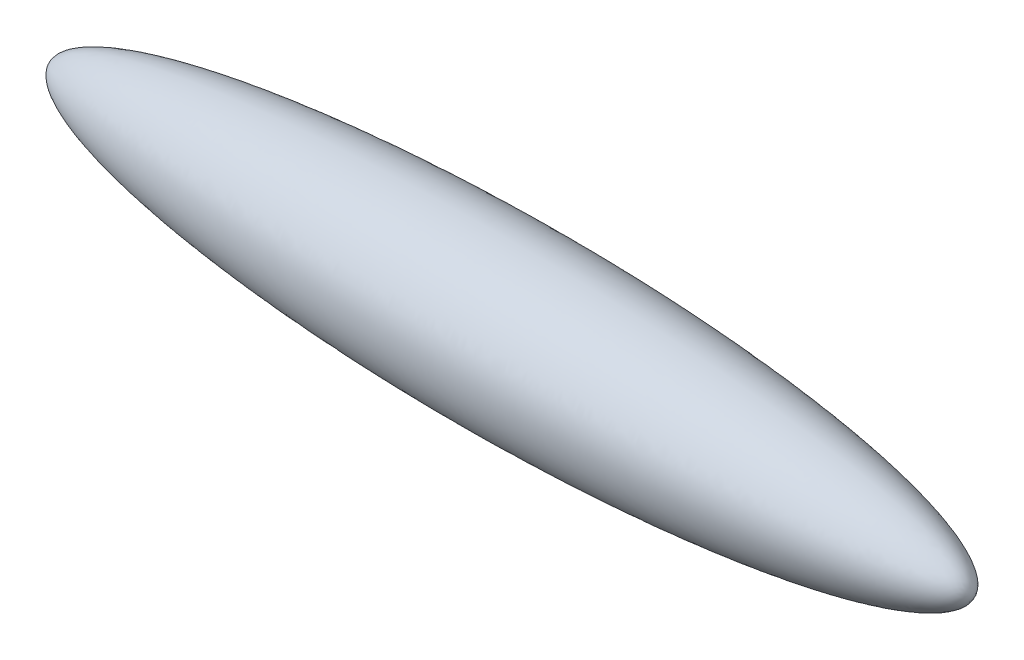
SolidWorks part; units mm, degrees
ref_plane "Plano frontal" through (0, 0, 0) normal (0, 0, 1) x (1, 0, 0)
ref_plane "Plano superior" through (0, 0, 0) normal (0, 1, 0) x (1, 0, 0)
ref_plane "Plano direito" through (0, 0, 0) normal (1, 0, 0) x (0, 0, -1)
ref_axis "Axis1" through (4.5739, 0, 0) along (-1, 0, 0)
sketch "Sketch3" plane through (0, 0, 0) normal (0, 0, 1) x (1, 0, 0)
  line L0 (686, 0) -> (-686, 0)
  spline S0 degree 4 poles (-686, 0) (-685.9997, 0.6998) (-685.9315, 2.0942) (-685.5565, 4.638) (-684.2628, 8.6049) (-681.9683, 12.7129) (-678.7283, 16.7962) (-674.2901, 21.2055) (-668.9242, 25.5245) (-663.2572, 29.309) (-657.4318, 32.6986) (-651.3994, 35.8922) (-643.1035, 39.9133) (-631.1855, 44.9636) (-615.5232, 50.6535) (-597.1722, 56.3985) (-578.3815, 61.5763) (-558.3108, 66.522) (-539.9291, 70.5832) (-523.2886, 73.9541) (-505.4444, 77.3208) (-487.5599, 80.4679) (-460.6708, 84.821) (-424.7132, 89.939) (-382.6513, 95.0696) (-334.4738, 99.9694) (-274.1554, 105.0481) (-201.6603, 109.6504) (-116.9816, 113.1179) (-32.2446, 114.5222) (40.3939, 114.3107) (100.9139, 113.1788) (149.3154, 111.6868) (197.6944, 109.5853) (246.0413, 106.8402) (294.3442, 103.4031) (342.5875, 99.2061) (390.7495, 94.1546) (432.7922, 88.8675) (468.7271, 83.5905) (498.5781, 78.5964) (522.3867, 74.1899) (546.1018, 69.302) (566.7424, 64.5181) (584.3238, 59.9673) (598.737, 55.8452) (610.0295, 52.3472) (621.0953, 48.608) (631.9085, 44.5842) (642.6336, 40.1258) (653.192, 35.112) (663.568, 29.2948) (672.4476, 23.0429) (679.1843, 16.6303) (683.2937, 10.6436) (685.2558, 5.9488) (685.8805, 2.7738) (685.9996, 0.9273) (686, 0) knots 0 0 0 0 0 0.001962 0.003923 0.007201 0.011661 0.015094 0.018527 0.024755 0.030984 0.034221 0.037459 0.043933 0.056883 0.070574 0.084265 0.097956 0.111647 0.128656 0.137161 0.145666 0.162675 0.179685 0.213703 0.247722 0.281741 0.315759 0.383797 0.451834 0.519872 0.553891 0.587909 0.621928 0.655947 0.689966 0.723984 0.758003 0.792022 0.82604 0.84305 0.860059 0.877068 0.894078 0.911087 0.919592 0.928097 0.936201 0.944306 0.95241 0.960515 0.968827 0.977139 0.985794 0.990965 0.994802 0.997401 1 1 1 1 1 construction
  spline S1 degree 4 poles (-686, 0) (-685.9997, 0.6998) (-685.9315, 2.0942) (-685.5565, 4.638) (-684.2628, 8.6049) (-681.9683, 12.7129) (-678.7283, 16.7962) (-674.2901, 21.2055) (-668.9242, 25.5245) (-663.2572, 29.309) (-657.4318, 32.6986) (-651.3994, 35.8922) (-643.1035, 39.9133) (-631.1855, 44.9636) (-615.5232, 50.6535) (-597.1722, 56.3985) (-578.3815, 61.5763) (-558.3108, 66.522) (-539.9291, 70.5832) (-523.2886, 73.9541) (-505.4444, 77.3208) (-487.5599, 80.4679) (-460.6708, 84.821) (-424.7132, 89.939) (-382.6513, 95.0696) (-334.4738, 99.9694) (-274.1554, 105.0481) (-201.6603, 109.6504) (-116.9816, 113.1179) (-32.2446, 114.5222) (40.3939, 114.3107) (100.9139, 113.1788) (149.3154, 111.6868) (197.6944, 109.5853) (246.0413, 106.8402) (294.3442, 103.4031) (342.5875, 99.2061) (390.7495, 94.1546) (432.7922, 88.8675) (468.7271, 83.5905) (498.5781, 78.5964) (522.3867, 74.1899) (546.1018, 69.302) (566.7424, 64.5181) (584.3238, 59.9673) (598.737, 55.8452) (610.0295, 52.3472) (621.0953, 48.608) (631.9085, 44.5842) (642.6336, 40.1258) (653.192, 35.112) (663.568, 29.2948) (672.4476, 23.0429) (679.1843, 16.6303) (683.2937, 10.6436) (685.2558, 5.9488) (685.8805, 2.7738) (685.9996, 0.9273) (686, 0) knots 0 0 0 0 0 0.001962 0.003923 0.007201 0.011661 0.015094 0.018527 0.024755 0.030984 0.034221 0.037459 0.043933 0.056883 0.070574 0.084265 0.097956 0.111647 0.128656 0.137161 0.145666 0.162675 0.179685 0.213703 0.247722 0.281741 0.315759 0.383797 0.451834 0.519872 0.553891 0.587909 0.621928 0.655947 0.689966 0.723984 0.758003 0.792022 0.82604 0.84305 0.860059 0.877068 0.894078 0.911087 0.919592 0.928097 0.936201 0.944306 0.95241 0.960515 0.968827 0.977139 0.985794 0.990965 0.994802 0.997401 1 1 1 1 1
revolve "Revolve7" add sketch "Sketch3" angle 360 about axis through (4.5739, 0, 0) along (-1, 0, 0)
